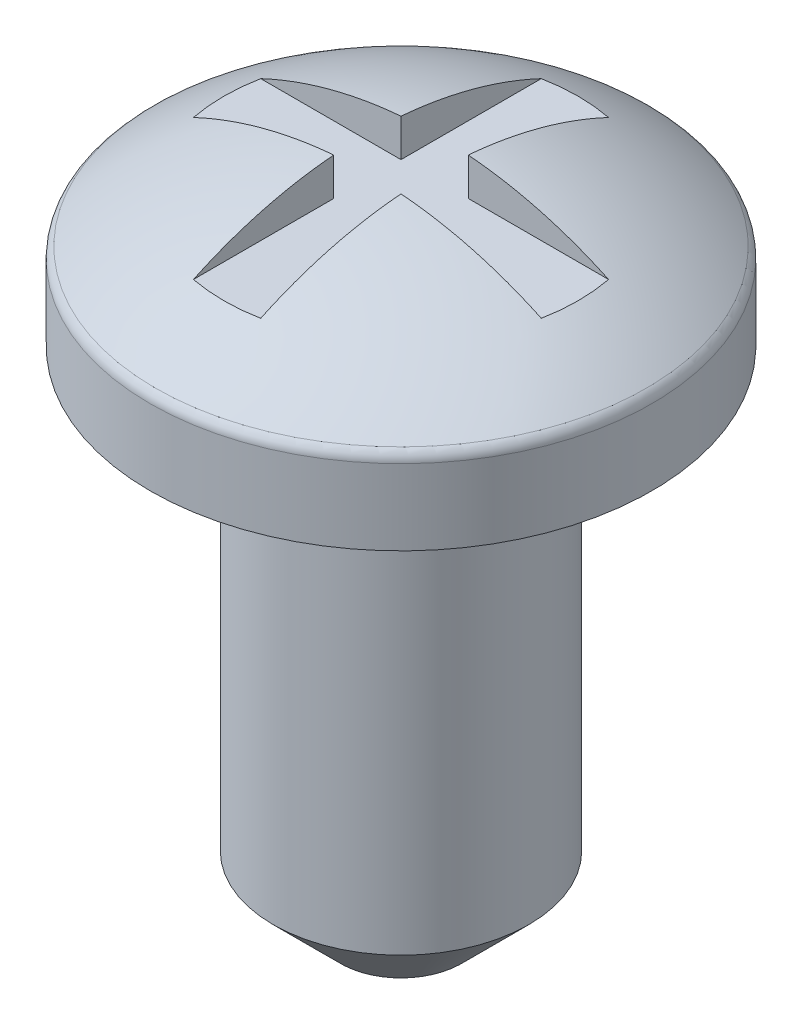
SolidWorks part; units mm, degrees
ref_plane "Front Plane" through (0, 0, 0) normal (0, 0, 1) x (1, 0, 0)
ref_plane "Top Plane" through (0, 0, 0) normal (0, 1, 0) x (1, 0, 0)
ref_plane "Right Plane" through (0, 0, 0) normal (1, 0, 0) x (0, 0, -1)
sketch "Sketch1" plane through (0, 0, 0) normal (0, 0, 1) x (1, 0, 0)
  line L0 (0, 0) -> (0, 12.7) construction
  line L1 (0, 0) -> (2.413, 0)
  line L2 (2.413, 0) -> (2.413, 9.525)
  line L3 (2.413, 9.525) -> (4.7371, 9.525)
  line L4 (4.7371, 9.525) -> (4.7371, 11.0762)
  line L6 (0, 0) -> (0, 12.7)
  arc A0 (0, 12.7) -> (4.7371, 11.0762) centre (0, 4.9784) cw
  dimension "D5" = 7.7216
  dimension "D1" = 12.7
  dimension "D2" = 4.826
  dimension "D3" = 9.4742
  dimension "D4" = 9.525
revolve "Revolve1" add sketch "Sketch1" angle 360 about L0
sketch "Sketch2" plane through (0, 0, 0) normal (0, 0, 1) x (1, 0, 0)
  line L0 (0, 12.7) -> (0, 11.938)
  line L1 (0, 11.938) -> (3.3447, 11.938)
  arc A0 (4.7371, 11.0762) -> (-4.7371, 11.0762) centre (0, 4.9784) ccw construction
  arc A1 (3.3447, 11.938) -> (0, 12.7) centre (0, 4.9784) ccw
  dimension "D1" = 0.762
extrude "Cut-Extrude1" cut sketch "Sketch2" against normal mid plane 1.27
pattern_circular "CirPattern1" count 4 over 360 about axis through (0, 0, 0) along (0, 1, 0) of "Cut-Extrude1"
chamfer "Chamfer1" distance 1.27 angle 45 1 edges at (0, 0, -2.413)
fillet "Fillet1" radius 0.254 1 edges at (0, 11.0762, -4.7371)
